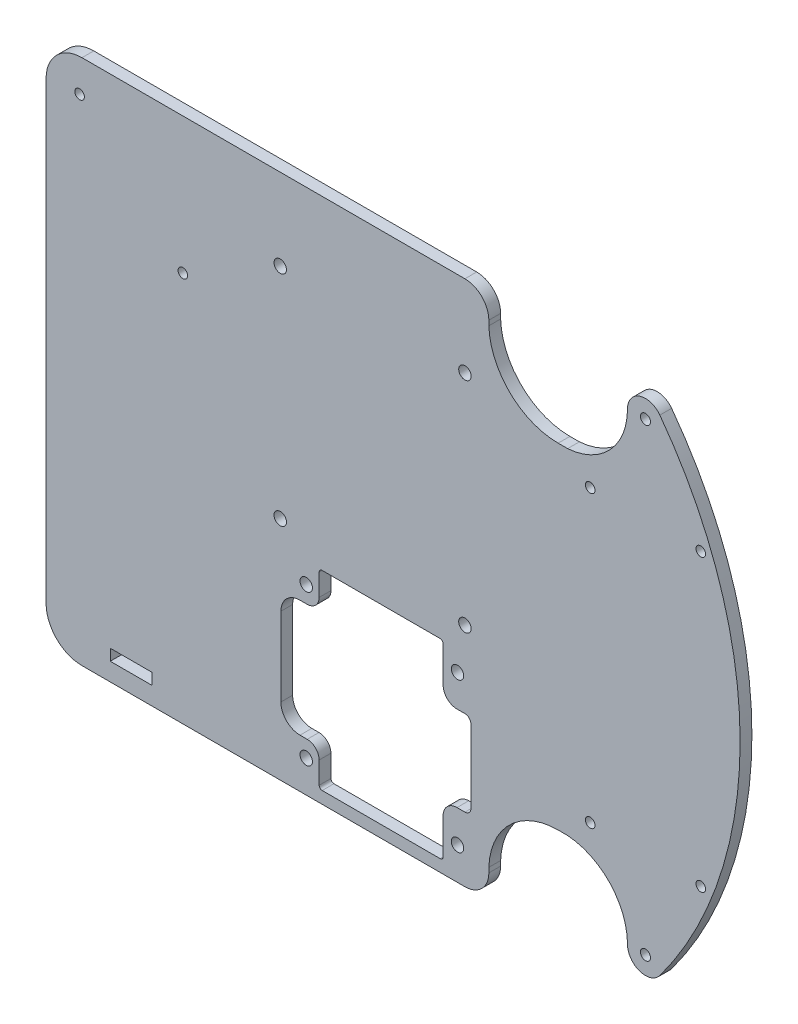
SolidWorks part; units mm, degrees
ref_plane "Alzado" through (0, 0, 0) normal (0, 0, 1) x (1, 0, 0)
ref_plane "Planta" through (0, 0, 0) normal (0, 1, 0) x (1, 0, 0)
ref_plane "Vista lateral" through (0, 0, 0) normal (1, 0, 0) x (0, 0, -1)
sketch "Croquis1" plane through (0, 0, 0) normal (0, 0, 1) x (1, 0, 0)
  line L1 (-92.075, -69.85) -> (92.075, -69.85)
  line L2 (-92.075, -69.85) -> (-92.075, 69.85)
  line L3 (-92.075, 69.85) -> (92.075, 69.85)
  line L4 (92.075, -69.85) -> (92.075, 69.85)
  line L5 (-92.075, -69.85) -> (92.075, 69.85) construction
  line L6 (-92.075, 69.85) -> (92.075, -69.85) construction
  point P0 (0, 0)
  dimension "D1" = 139.7
  dimension "D2" = 184.15
extrude "Saliente-Extruir1" add sketch "Croquis1" along normal blind 3.1242
sketch "Croquis2" plane through (0, 0, 3.1242) normal (0, 0, 1) x (1, 0, 0)
  line L0 (-92.075, -69.85) -> (92.075, -69.85) construction
  line L1 (92.075, 69.85) -> (31.75, 69.85)
  line L2 (92.075, 69.85) -> (92.075, -69.85)
  line L3 (92.075, -69.85) -> (31.75, -69.85)
  line L4 (31.75, 69.85) -> (31.75, -69.85)
  line L5 (0, 0) -> (92.075, 0) construction
  line L6 (57.5056, 69.85) -> (66.3194, 69.85)
  line L7 (57.5056, 69.85) -> (57.5056, 52.4764)
  line L8 (57.5056, 52.4764) -> (66.3194, 52.4764)
  line L9 (66.3194, 69.85) -> (66.3194, 52.4764)
  line L10 (66.3194, -69.85) -> (66.3194, -52.4764)
  line L11 (57.5056, -52.4764) -> (66.3194, -52.4764)
  line L12 (57.5056, -69.85) -> (57.5056, -52.4764)
  line L13 (57.5056, -69.85) -> (66.3194, -69.85)
  circle A0 centre (66.9544, 61.5442) radius 2.921
  circle A1 centre (66.9544, 61.5442) radius 1.3335
  circle A2 centre (66.9544, -61.5442) radius 1.3335
  circle A3 centre (66.9544, -61.5442) radius 2.921
  point P11 (61.9125, 69.85)
  point P12 (61.9125, 52.4764)
  point P13 (66.9544, 58.6232)
  point P14 (69.8754, 61.5442)
  point P28 (69.8754, -61.5442)
  point P29 (66.9544, -58.6232)
  point P30 (61.9125, -52.4764)
  point P31 (61.9125, -69.85)
  point P32 (66.9544, -60.2107)
  point P33 (66.9544, 60.2107)
  point P34 (66.9544, -62.8777)
  point P35 (66.9544, 62.8777)
  dimension "D3" = 5.842
  dimension "D4" = 1.5875
  dimension "D1" = 60.325
  dimension "D2" = 8.8138
  dimension "D5" = 3.556
  dimension "D6" = 17.3736
  dimension "D7" = 6.1468
  dimension "D8" = 120.4214
  dimension "D9" = 125.7554
extrude "Cortar-Extruir1" cut sketch "Croquis2" against normal through all contours L9 A1 | L9 A1 | A2
sketch "Croquis9" plane through (0, 0, 3.1242) normal (0, 0, 1) x (1, 0, 0)
  line L0 (52.2859, 38.4937) -> (81.6229, 38.4937) construction
  line L1 (0, 0) -> (92.075, 0) construction
  line L2 (92.075, -69.85) -> (92.075, 69.85) construction
  line L3 (52.2859, -38.4937) -> (81.6229, -38.4937) construction
  circle A0 centre (52.2859, 38.4937) radius 1.27
  circle A1 centre (81.6229, 38.4937) radius 1.27
  circle A2 centre (81.6229, 38.4937) radius 2.794
  circle A3 centre (66.9544, 61.5442) radius 1.3335 construction
  circle A4 centre (66.9544, 61.5442) radius 1.3335
  circle A5 centre (81.6229, -38.4937) radius 1.27
  circle A6 centre (52.2859, -38.4937) radius 1.27
  point P4 (66.9544, 62.8777)
  point P5 (81.6229, 35.6997)
  point P9 (66.9544, 38.4937)
  point P22 (81.6229, -35.6997)
  dimension "D1" = 29.337
  dimension "D2" = 2.54
  dimension "D3" = 27.178
  dimension "D4" = 5.588
extrude "Cortar-Extruir6" cut sketch "Croquis9" against normal through all
sketch "Croquis3" plane through (0, 0, 3.1242) normal (0, 0, 1) x (1, 0, 0)
  line L0 (92.075, -69.85) -> (92.075, 69.85) construction
  line L1 (92.075, 69.85) -> (-92.075, 69.85) construction
  line L2 (0, 0) -> (92.075, 0) construction
  line L3 (25.4, 69.85) -> (62.1919, 69.85)
  line L4 (25.4, 69.85) -> (25.4, 44.45)
  line L5 (25.4, 44.45) -> (62.1919, 44.45)
  line L6 (62.1919, 69.85) -> (62.1919, 44.45)
  line L7 (62.1919, -69.85) -> (62.1919, -44.45)
  line L8 (25.4, -44.45) -> (62.1919, -44.45)
  line L9 (25.4, -69.85) -> (25.4, -44.45)
  line L10 (25.4, -69.85) -> (62.1919, -69.85)
  line L11 (-92.075, -69.85) -> (92.075, -69.85) construction
  line L12 (-82.55, 69.85) -> (0, 69.85)
  line L13 (-92.075, 60.325) -> (-92.075, -60.325)
  line L14 (-82.55, -69.85) -> (0, -69.85)
  line L15 (0, 69.85) -> (0, -69.85)
  circle A0 centre (66.9544, 61.5442) radius 4.7625
  arc A1 (70.7775, 64.3842) -> (70.7775, -64.3842) centre (-15.8931, 0) cw
  arc A2 (43.7959, 44.45) -> (62.1919, 61.5442) centre (45.0516, 61.5442) ccw
  arc A3 (19.05, 69.85) -> (25.4, 63.5) centre (19.05, 63.5) cw
  arc A4 (25.4, 63.5) -> (43.7959, 44.45) centre (43.7959, 62.8572) ccw
  arc A5 (25.4, -63.5) -> (43.7959, -44.45) centre (43.7959, -62.8572) cw
  arc A6 (19.05, -69.85) -> (25.4, -63.5) centre (19.05, -63.5) ccw
  arc A7 (43.7959, -44.45) -> (62.1919, -61.5442) centre (45.0516, -61.5442) cw
  circle A8 centre (66.9544, -61.5442) radius 4.7625
  arc A9 (-92.075, -60.325) -> (-82.55, -69.85) centre (-82.55, -60.325) ccw
  arc A10 (-82.55, 69.85) -> (-92.075, 60.325) centre (-82.55, 60.325) ccw
  point P48 (-92.075, 69.85)
  dimension "D1" = 25.4
  dimension "D3" = 6.35
  dimension "D4" = 9.525
  dimension "D5" = 9.525
  dimension "D2" = 25.4
extrude "Cortar-Extruir2" cut sketch "Croquis3" against normal through all
sketch "Croquis5" plane through (0, 0, 3.1242) normal (0, 0, 1) x (1, 0, 0)
  line L0 (-82.55, -69.85) -> (19.05, -69.85) construction
  line L1 (-29.7815, -16.1036) -> (20.6375, -16.1036)
  line L2 (-29.7815, -16.1036) -> (-29.7815, -66.675)
  line L3 (-29.7815, -66.675) -> (20.6375, -66.675)
  line L4 (20.6375, -16.1036) -> (20.6375, -66.675)
  line L5 (-29.7815, -41.3893) -> (20.6375, -41.3893) construction
  line L6 (25.4, -63.5) -> (25.4, -62.2144) construction
  line L7 (20.6375, -66.675) -> (13.2715, -66.675)
  line L8 (20.6375, -66.675) -> (20.6375, -16.1036)
  line L9 (20.6375, -16.1036) -> (13.2715, -16.1036)
  line L10 (13.2715, -66.675) -> (13.2715, -16.1036)
  line L11 (-29.7815, -16.1036) -> (-19.6215, -16.1036)
  line L12 (-29.7815, -16.1036) -> (-29.7815, -66.675)
  line L13 (-29.7815, -66.675) -> (-19.6215, -66.675)
  line L14 (-19.6215, -16.1036) -> (-19.6215, -66.675)
  line L15 (13.2715, -30.0736) -> (20.6375, -30.0736)
  line L16 (13.2715, -30.0736) -> (13.2715, -52.705)
  line L17 (13.2715, -52.705) -> (20.6375, -52.705)
  line L18 (20.6375, -30.0736) -> (20.6375, -52.705)
  line L19 (-19.6215, -25.8826) -> (-29.7815, -25.8826)
  line L20 (-19.6215, -25.8826) -> (-19.6215, -56.896)
  line L21 (-19.6215, -56.896) -> (-29.7815, -56.896)
  line L22 (-29.7815, -25.8826) -> (-29.7815, -56.896)
  circle A0 centre (17.0815, -21.5646) radius 1.651
  circle A1 centre (-23.0505, -21.4376) radius 1.651
  circle A2 centre (17.0815, -61.214) radius 1.651
  circle A3 centre (-23.0505, -61.341) radius 1.651
  arc A4 (19.05, -52.705) -> (20.6375, -51.1175) centre (19.05, -51.1175) ccw
  arc A5 (16.9545, -52.705) -> (13.2715, -56.388) centre (16.9545, -56.388) ccw
  arc A6 (-24.7015, -56.896) -> (-29.7815, -51.816) centre (-24.7015, -51.816) cw
  arc A7 (-22.7965, -56.896) -> (-19.6215, -60.071) centre (-22.7965, -60.071) cw
  arc A8 (19.05, -30.0736) -> (20.6375, -31.6611) centre (19.05, -31.6611) cw
  arc A9 (16.9545, -30.0736) -> (13.2715, -26.3906) centre (16.9545, -26.3906) cw
  arc A10 (-24.7015, -25.8826) -> (-29.7815, -30.9626) centre (-24.7015, -30.9626) ccw
  arc A11 (-22.7965, -25.8826) -> (-19.6215, -22.7076) centre (-22.7965, -22.7076) ccw
  arc A12 (-19.6215, -16.8973) -> (-18.8278, -16.1036) centre (-18.8278, -16.8973) cw
  arc A13 (12.4778, -16.1036) -> (13.2715, -16.8973) centre (12.4778, -16.8973) cw
  arc A14 (12.4778, -66.675) -> (13.2715, -65.8813) centre (12.4778, -65.8813) ccw
  arc A15 (-19.6215, -65.8813) -> (-18.8278, -66.675) centre (-18.8278, -65.8813) ccw
  point P4 (18.7325, -21.5646)
  point P5 (17.0815, -19.9136)
  point P6 (-23.0505, -19.7866)
  point P14 (-24.7015, -21.4376)
  dimension "D5" = 3.302
  dimension "D16" = 1.5875
  dimension "D17" = 3.175
  dimension "D18" = 0.7937
  dimension "D1" = 50.5714
  dimension "D2" = 50.419
  dimension "D3" = 3.81
  dimension "D4" = 1.905
  dimension "D6" = 3.175
  dimension "D7" = 4.7625
  dimension "D8" = 5.08
  dimension "D9" = 3.683
  dimension "D10" = 7.366
  dimension "D11" = 10.16
  dimension "D12" = 13.97
  dimension "D13" = 13.97
  dimension "D14" = 9.779
  dimension "D15" = 9.779
extrude "Driver" cut sketch "Croquis5" against normal through all contours L22 L5 L14 L19 A10 | L5 L12 A6 L21 L20 | L14 L5 L16 L10 L1 | L16 L5 L18 A8 L15 | L5 L10 L17 A4 L8 | L5 L20 L14 L3 L10 | A5 L17 L10 | L21 A7 L14 | A11 L19 L14 | L15 A9 L10 | A1 | A3 | A2 | A0
sketch "Croquis6" plane through (0, 0, 3.1242) normal (0, 0, 1) x (1, 0, 0)
  line L0 (-33.45, 19.2464) -> (22.55, 19.2464)
  line L1 (-29.95, 48.2464) -> (19.05, 48.2464)
  line L2 (-29.95, 48.2464) -> (-29.95, -9.7536)
  line L3 (-29.95, -9.7536) -> (19.05, -9.7536)
  line L4 (19.05, 48.2464) -> (19.05, -9.7536)
  line L5 (-18.8278, -16.1036) -> (12.4778, -16.1036) construction
  line L6 (-5.45, -9.7536) -> (-5.45, 74.0664)
  line L7 (25.4, 63.5) -> (25.4, 62.2144) construction
  circle A0 centre (-29.95, 48.2464) radius 1.651
  circle A1 centre (19.05, 48.2464) radius 1.651
  circle A2 centre (19.05, -9.7536) radius 1.651
  circle A3 centre (-29.95, -9.7536) radius 1.651
  point P13 (-5.45, 19.2464)
  point P14 (19.05, 19.2464)
  point P16 (-5.45, 48.2464)
  dimension "D1" = 3.302
  dimension "D2" = 58
  dimension "D3" = 49
  dimension "D4" = 56
  dimension "D5" = 6.35
  dimension "D6" = 6.35
  dimension "D7" = 83.82
extrude "RasPi" cut sketch "Croquis6" against normal through all contours A3 | A2 | A1 | A0
sketch "Croquis8" plane through (0, 0, 3.1242) normal (0, 0, 1) x (1, 0, 0)
  line L0 (-83.185, 61.138) -> (-55.7952, 33.7483)
  line L3 (-83.185, 61.138) -> (-55.7952, 61.138)
  line L4 (-83.185, 61.138) -> (-83.185, 33.7483)
  line L5 (-83.185, 33.7483) -> (-55.7952, 33.7483)
  line L6 (-55.7952, 61.138) -> (-55.7952, 33.7483)
  line L7 (-92.075, 60.325) -> (-92.075, -60.325) construction
  circle A0 centre (-83.185, 61.138) radius 1.27
  circle A1 centre (-55.7952, 33.7483) radius 1.27
  dimension "D1" = 8.89
  dimension "D3" = 2.54
  dimension "D4" = 2.54
  dimension "D2" = 38.735
extrude "Cortar-Extruir5" cut sketch "Croquis8" against normal through all contours A0 | A1
sketch "Croquis7" plane through (0, 0, 3.1242) normal (0, 0, 1) x (1, 0, 0)
  line L0 (-69.4901, 33.7483) -> (-69.4901, -62.0903) construction
  line L1 (-75.0464, -62.0903) -> (-63.9339, -62.0903)
  line L2 (-75.0464, -62.0903) -> (-75.0464, -65.0875)
  line L3 (-75.0464, -65.0875) -> (-63.9339, -65.0875)
  line L4 (-63.9339, -62.0903) -> (-63.9339, -65.0875)
  line L5 (-83.185, 61.138) -> (-55.7952, 61.138)
  line L6 (-83.185, 61.138) -> (-83.185, 33.7483)
  line L7 (-83.185, 33.7483) -> (-55.7952, 33.7483)
  line L8 (-55.7952, 61.138) -> (-55.7952, 33.7483)
  line L9 (-82.55, -69.85) -> (19.05, -69.85) construction
  dimension "D1" = 2.9972
  dimension "D2" = 11.1125
  dimension "D3" = 4.7625
extrude "Cortar-Extruir7" cut sketch "Croquis7" against normal through all contours L3 L4 L1 L2
